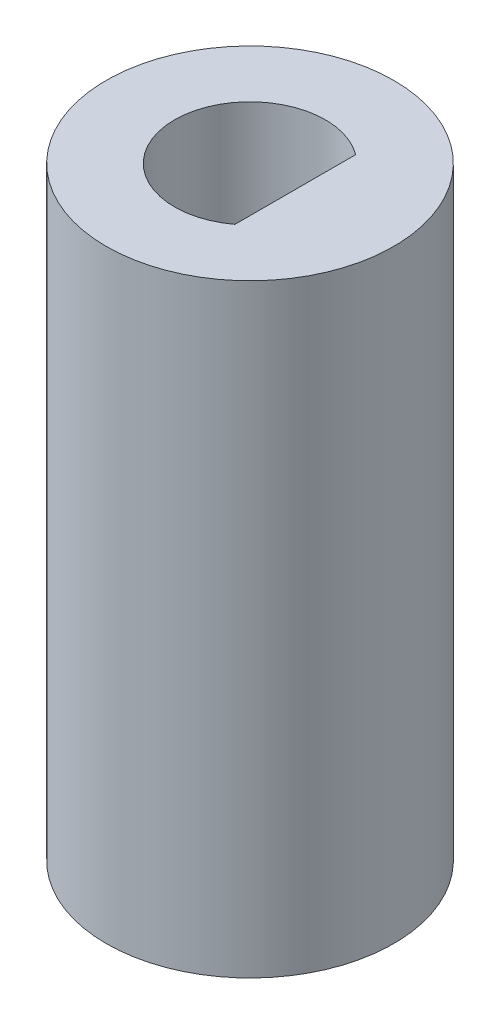
SolidWorks part; units mm, degrees
ref_plane "Front Plane" through (0, 0, 0) normal (0, 0, 1) x (1, 0, 0)
ref_plane "Top Plane" through (0, 0, 0) normal (0, 1, 0) x (1, 0, 0)
ref_plane "Right Plane" through (0, 0, 0) normal (1, 0, 0) x (0, 0, -1)
sketch "Sketch1" plane through (0, 0, 0) normal (0, 1, 0) x (1, 0, 0)
  circle A0 centre (0, 0) radius 4.7625
  dimension "D1" = 9.525
extrude "Boss-Extrude1" add sketch "Sketch1" along normal blind 20
sketch "Sketch2" plane through (0, 20, 0) normal (0, 1, 0) x (1, 0, 0)
  line L0 (1.5, 2) -> (1.5, -2)
  arc A0 (1.5, 2) -> (1.5, -2) centre (0, 0) ccw
  arc A1 (1.5, -2) -> (1.5, 2) centre (0, 0) ccw construction
  dimension "D1" = 5
  dimension "D2" = 1.5
extrude "Cut-Extrude1" cut sketch "Sketch2" against normal blind 7
sketch "Sketch3" plane through (0, 0, 0) normal (0, -1, 0) x (1, 0, 0)
  line L0 (0.9766, 1.2516) -> (0.9766, -1.2516)
  circle A0 centre (0, 0) radius 1.5875
  dimension "D1" = 3.175
extrude "Cut-Extrude2" cut sketch "Sketch3" against normal blind 11 contours A0
